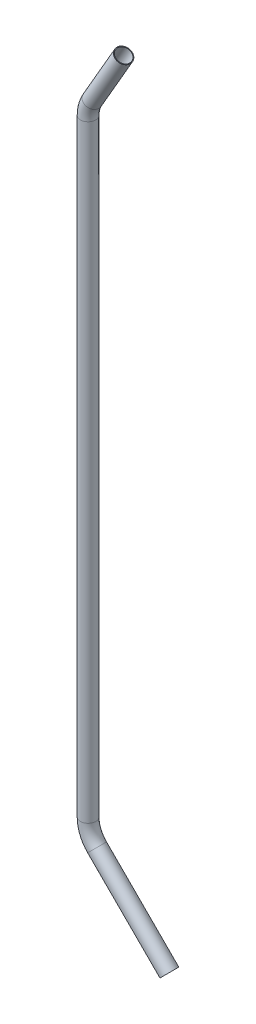
SolidWorks part; units mm, degrees
ref_plane "Front Plane" through (0, 0, 0) normal (0, 0, 1) x (1, 0, 0)
ref_plane "Top Plane" through (0, 0, 0) normal (0, 1, 0) x (1, 0, 0)
ref_plane "Right Plane" through (0, 0, 0) normal (1, 0, 0) x (0, 0, -1)
sketch "Sketch1" plane through (0, 0, 0) normal (0, 0, 1) x (1, 0, 0)
  line L0 (0, -253.638) -> (0, -196.488) construction
  line L2 (0, -196.488) -> (-111.76, -196.488) construction
  line L3 (-111.76, -196.488) -> (-111.76, 693.0535) construction
  line L4 (-111.76, 693.0535) -> (-67.7659, 769.2535) construction
  line L5 (0, -196.488) -> (-111.76, -84.728) construction
  line L7 (-11.1592, -185.3288) -> (-100.6008, -95.8873)
  line L8 (-111.76, -68.9465) -> (-111.76, 682.8446)
  line L9 (-106.6556, 701.8946) -> (-67.7659, 769.2535)
  arc A1 (-111.76, -68.9465) -> (-100.6008, -95.8873) centre (-73.66, -68.9465) ccw
  arc A2 (-111.76, 682.8446) -> (-106.6556, 701.8946) centre (-73.66, 682.8446) cw
  dimension "D6" = 38.1
  dimension "D9" = 38.1
  dimension "D1" = 30
  dimension "D2" = 45
  dimension "D3" = 57.15
  dimension "D4" = 111.76
  dimension "D7" = 76.2
  dimension "D8" = 762
sketch "Sketch2" plane through (0, 0, 0) normal (0, 1, 0) x (1, 0, 0)
  circle A1 centre (-111.76, 0) radius 9.525
  circle A2 centre (-111.76, 0) radius 8.7122
  dimension "D1" = 19.05
  dimension "D2" = 0.8128
sweep "Sweep1" add profiles "Sketch2" path "Sketch1"
